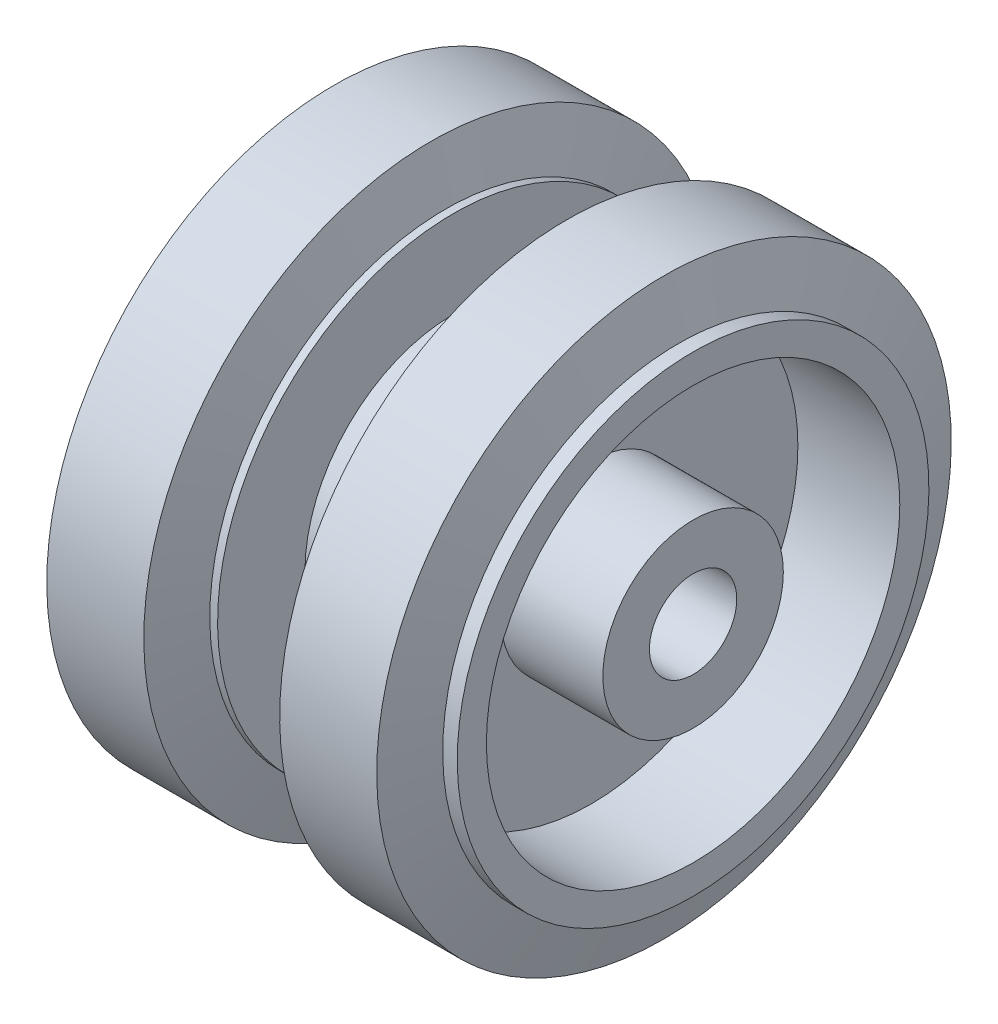
SolidWorks part; units mm, degrees
ref_plane "Front Plane" through (0, 0, 0) normal (0, 0, 1) x (1, 0, 0)
ref_plane "Top Plane" through (0, 0, 0) normal (0, 1, 0) x (1, 0, 0)
ref_plane "Right Plane" through (0, 0, 0) normal (1, 0, 0) x (0, 0, -1)
sketch "Sketch1" plane through (0, 0, 0) normal (0, 0, 1) x (1, 0, 0)
  line L0 (0, 0) -> (0, 15.3)
  line L1 (0, 15.3) -> (-4.7, 15.3)
  line L2 (-4.7, 15.3) -> (-4.7, 24.3)
  line L5 (-7, 29.6) -> (-17, 29.6)
  line L6 (-17, 29.6) -> (-18.5, 24.3)
  line L7 (-18.5, 24.3) -> (-20, 24.3)
  line L8 (-20, 24.3) -> (-20, 0)
  line L10 (-20, 0) -> (0, 0) construction
  line L11 (-4.7, 24.3) -> (-5.5, 24.3)
  line L12 (-5.5, 24.3) -> (-7, 29.6)
  line L13 (0, 0) -> (-20, 0)
  dimension "D1" = 4.7
  dimension "D2" = 10
  dimension "D3" = 1.5
  dimension "D4" = 3
  dimension "D5" = 0.8
  dimension "D6" = 2.3
  dimension "D7" = 24.3
  dimension "D8" = 29.6
  dimension "D9" = 15.3
revolve "Revolve1" add sketch "Sketch1" angle 360 about L10
sketch "Sketch2" plane through (0, 0, 0) normal (0, 0, 1) x (1, 0, 0)
  line L0 (0, 0) -> (-260.553, 0) construction
  line L1 (-20, 24.3) -> (-20, -24.3) construction
  line L2 (-20, 21.3) -> (-9.5, 21.3)
  line L3 (-20, 21.3) -> (-20, 9.3)
  line L4 (-20, 9.3) -> (-9.5, 9.3)
  line L5 (-9.5, 21.3) -> (-9.5, 9.3)
  line L7 (-20, 4.5) -> (-5, 4.5)
  line L8 (-20, 4.5) -> (-20, 0)
  line L9 (-20, 0) -> (-5, 0)
  line L10 (-5, 4.5) -> (-5, 0)
  dimension "D1" = 10.5
  dimension "D2" = 9.3
  dimension "D3" = 21.3
  dimension "D4" = 15
  dimension "D5" = 4.5
revolve "Cut-Revolve1" cut sketch "Sketch2" angle 360 about L0
mirror "Mirror1" about plane through (0, 0, 0) normal (-1, 0, 0) of "Cut-Revolve1", "Revolve1"
